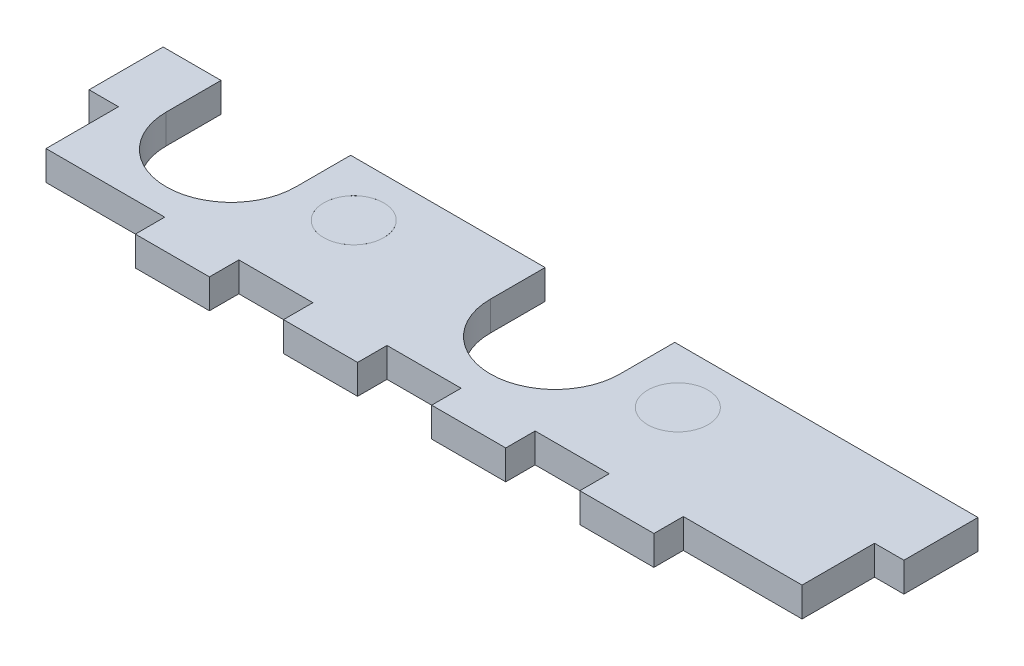
SolidWorks part; units mm, degrees
ref_plane "Front Plane" through (0, 0, 0) normal (0, 0, 1) x (1, 0, 0)
ref_plane "Top Plane" through (0, 0, 0) normal (0, 1, 0) x (1, 0, 0)
ref_plane "Right Plane" through (0, 0, 0) normal (1, 0, 0) x (0, 0, -1)
sketch "Sketch3" plane through (0, 0, 0) normal (0, 1, 0) x (1, 0, 0)
  line L1 (0, 0) -> (88, 0)
  line L2 (0, 0) -> (0, -30)
  line L3 (0, -30) -> (88, -30)
  line L4 (88, 0) -> (88, -30)
  dimension "D1" = 30
  dimension "D2" = 88
extrude "Boss-Extrude1" add sketch "Sketch3" along normal blind 3.175
sketch "Sketch4" plane through (0, 3.175, 0) normal (0, 1, 0) x (1, 0, 0)
  line L0 (44, 0) -> (44, -30) construction
  line L1 (88, 0) -> (0, 0) construction
  line L2 (0, -30) -> (88, -30) construction
  line L3 (0, -15) -> (88, -15) construction
  line L4 (0, 0) -> (0, -30) construction
  line L5 (88, -30) -> (88, 0) construction
  line L6 (16, -30) -> (16, -26.825)
  line L7 (40, -30) -> (48, -30)
  line L8 (0, -26.825) -> (16, -26.825)
  line L9 (40, -26.825) -> (48, -26.825)
  line L10 (48, -30) -> (48, -26.825)
  line L11 (56, -30) -> (64, -30)
  line L12 (56, -30) -> (56, -26.825)
  line L13 (56, -26.825) -> (64, -26.825)
  line L14 (64, -30) -> (64, -26.825)
  line L15 (88, -30) -> (72, -30)
  line L16 (88, -30) -> (88, -26.825)
  line L17 (88, -26.825) -> (72, -26.825)
  line L18 (72, -30) -> (72, -26.825)
  line L19 (0, -30) -> (0, -26.825)
  line L20 (0, -30) -> (16, -30)
  line L21 (24, -30) -> (24, -26.825)
  line L22 (32, -26.825) -> (24, -26.825)
  line L23 (32, -30) -> (32, -26.825)
  line L24 (32, -30) -> (24, -30)
  line L25 (40, -30) -> (40, -26.825)
  line L26 (88, -19) -> (88, -26.825)
  line L27 (0, 0) -> (3.175, 0)
  line L28 (0, 0) -> (0, -11)
  line L29 (0, -11) -> (3.175, -11)
  line L30 (3.175, 0) -> (3.175, -11)
  line L31 (84.825, -19) -> (84.825, -26.825)
  line L32 (88, -19) -> (84.825, -19)
  line L33 (84.825, 0) -> (84.825, -11)
  line L34 (88, -11) -> (84.825, -11)
  line L35 (0, -19) -> (3.175, -19)
  line L36 (0, -19) -> (0, -26.825)
  line L37 (0, -26.825) -> (3.175, -26.825)
  line L38 (3.175, -19) -> (3.175, -26.825)
  line L39 (88, 0) -> (88, -11)
  line L40 (88, 0) -> (84.825, 0)
  line L41 (84.825, -26.825) -> (88, -26.825)
  line L42 (88, -19) -> (88, -26.825)
  point P34 (44, -26.825)
  line M11 (0, 0) -> (0, -30)
  line M12 (0, -30) -> (88, -30)
  line M13 (88, -30) -> (88, 0)
  line M14 (88, 0) -> (0, 0)
  dimension "D1" = 4
  dimension "D2" = 3.175
  dimension "D3" = 8
  dimension "D4" = 3.175
  dimension "D5" = 8
  dimension "D6" = 3.175
  dimension "D7" = 8
  dimension "D8" = 8
extrude "Cut-Extrude1" cut sketch "Sketch4" against normal up to next contours L38 L35 L8 M11 | L8 L6 M11 M12 | L23 L22 L21 M12 | L25 L10 L9 M12 | L14 L13 L12 M12 | L32 L31 L17 M13 | L34 L33 M13 M14 | L18 L17 M12 M13 | L30 L29 M14 M11
sketch "Sketch5" plane through (0, 3.175, 0) normal (0, 1, 0) x (1, 0, 0)
  line L0 (0, -16.915) -> (88, -16.915) construction
  line L1 (0, -11) -> (0, -19) construction
  line L2 (88, -19) -> (88, -11) construction
  line L3 (32, -26.825) -> (24, -26.825) construction
  line L4 (44, 0) -> (44, -26.825) construction
  line L5 (84.825, 0) -> (3.175, 0) construction
  line L6 (40, -26.825) -> (48, -26.825) construction
  circle A0 centre (61.5, -16.915) radius 3.25
  circle A1 centre (26.5, -16.915) radius 3.25
  point P16 (44, -16.915)
  dimension "D2" = 6.5
  dimension "D1" = 9.91
  dimension "D3" = 17.5
extrude "Cut-Extrude2" cut sketch "Sketch5" against normal up to next
sketch "Sketch6" plane through (0, 3.175, 0) normal (0, 1, 0) x (1, 0, 0)
  line L1 (3.175, -11) -> (84.825, -11)
  line L2 (3.175, -11) -> (3.175, 0)
  line L3 (3.175, 0) -> (84.825, 0)
  line L4 (84.825, -11) -> (84.825, 0)
extrude "Cut-Extrude3" cut sketch "Sketch6" against normal up to next
sketch "Sketch7" plane through (0, 3.175, 0) normal (0, 1, 0) x (1, 0, 0)
  line L0 (44, -11) -> (44, -26.825) construction
  line L1 (88, -11) -> (0, -11) construction
  line L2 (40, -26.825) -> (48, -26.825) construction
  line L3 (0, -16.915) -> (88, -16.915) construction
  line L4 (0, -11) -> (0, -19) construction
  line L5 (88, -19) -> (88, -11) construction
  line L6 (6.25, -16.915) -> (6.25, -11)
  line L7 (20.25, -16.915) -> (20.25, -11)
  line L8 (26.5, -13.665) -> (26.5, -20.165) construction
  line L9 (41.25, -16.915) -> (41.25, -11)
  line L10 (55.25, -16.915) -> (55.25, -11)
  line L11 (6.25, -11) -> (20.25, -11)
  line L12 (41.25, -11) -> (55.25, -11)
  line L13 (61.5, -13.665) -> (61.5, -20.165) construction
  circle A0 centre (26.5, -16.915) radius 3.25 construction
  arc A2 (6.25, -16.915) -> (20.25, -16.915) centre (13.25, -16.915) ccw
  arc A3 (41.25, -16.915) -> (55.25, -16.915) centre (48.25, -16.915) ccw
  point P15 (13.25, -16.915)
  point P16 (6.25, -16.915)
  point P28 (48.25, -16.915)
  point P29 (41.25, -16.915)
  dimension "D1" = 13.25
  dimension "D2" = 7
  dimension "D3" = 2
extrude "Cut-Extrude4" cut sketch "Sketch7" against normal up to next
sketch "Sketch8" plane through (0, 3.175, 0) normal (0, 1, 0) x (1, 0, 0)
  circle A0 centre (26.5, -16.915) radius 3.25
  circle A1 centre (61.5, -16.915) radius 3.25
extrude "Boss-Extrude2" add sketch "Sketch8" against normal blind 3.175 separate body
